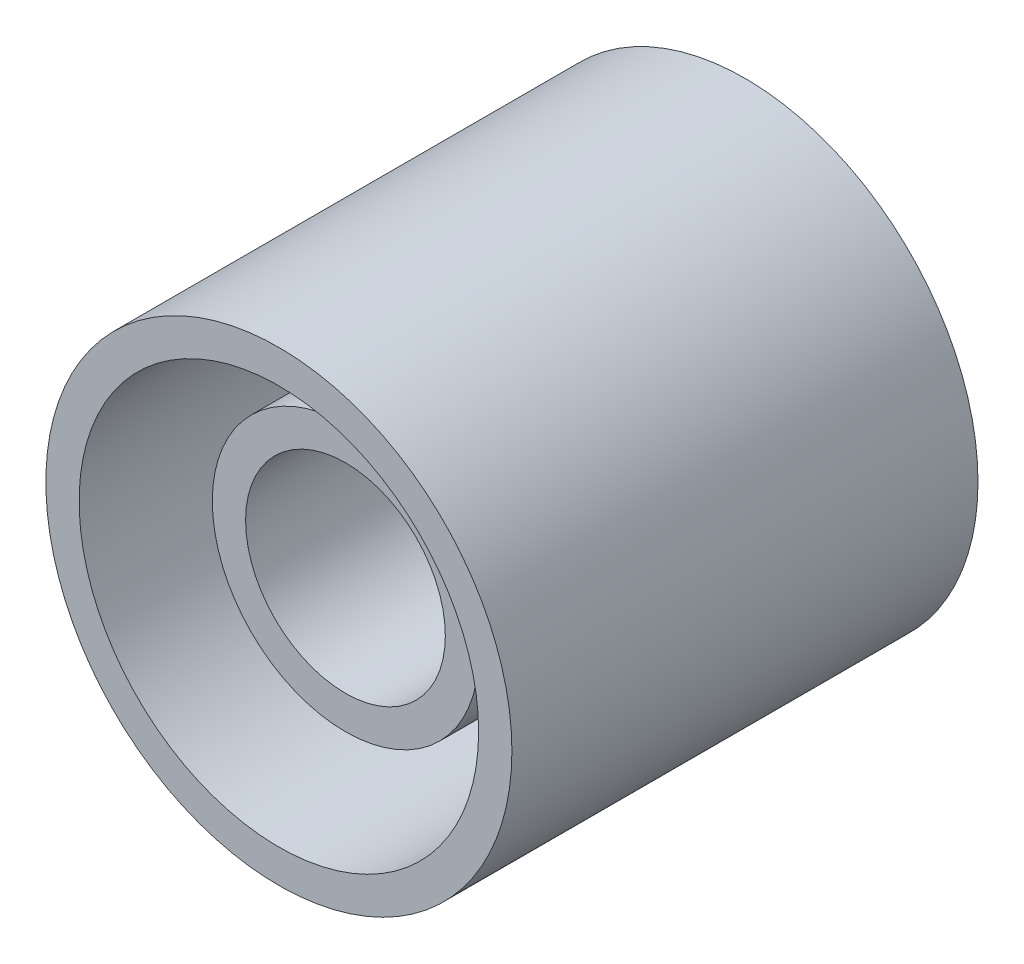
SolidWorks part; units mm, degrees
ref_plane "Front Plane" through (0, 0, 0) normal (0, 0, 1) x (1, 0, 0)
ref_plane "Top Plane" through (0, 0, 0) normal (0, 1, 0) x (1, 0, 0)
ref_plane "Right Plane" through (0, 0, 0) normal (1, 0, 0) x (0, 0, -1)
sketch "Sketch3" plane through (0, 0, 0) normal (0, 0, 1) x (1, 0, 0)
  circle A0 centre (0, 0) radius 1.75
  dimension "D1" = 3.5
extrude "Boss-Extrude1" add sketch "Sketch3" along normal blind 3.5
sketch "Sketch4" plane through (0, 0, 3.5) normal (0, 0, 1) x (1, 0, 0)
  circle A0 centre (0, 0) radius 0.75
  dimension "D1" = 1.5
extrude "Cut-Extrude1" cut sketch "Sketch4" against normal blind 3
sketch "Sketch6" plane through (0, 0, 3.5) normal (0, 0, 1) x (1, 0, 0)
  circle A0 centre (0, 0) radius 1
  circle A1 centre (0, 0) radius 1.5
  dimension "D1" = 2
  dimension "D2" = 3
extrude "Cut-Extrude6" cut sketch "Sketch6" against normal blind 3
sketch "Sketch10" plane through (0, 0, 3.5) normal (0, 0, 1) x (1, 0, 0)
  circle A0 centre (0, 0) radius 1
  dimension "D1" = 2
extrude "Cut-Extrude7" cut sketch "Sketch10" against normal blind 0.5
sketch "Sketch11" plane through (0, 0, 3.5) normal (0, 0, 1) x (1, 0, 0)
sketch "Sketch12" plane through (0, 0, 0) normal (0, 0, -1) x (-1, 0, 0)
  circle A0 centre (0, 0) radius 1.5
  dimension "D1" = 3
extrude "Cut-Extrude8" cut sketch "Sketch12" against normal blind 0.3
